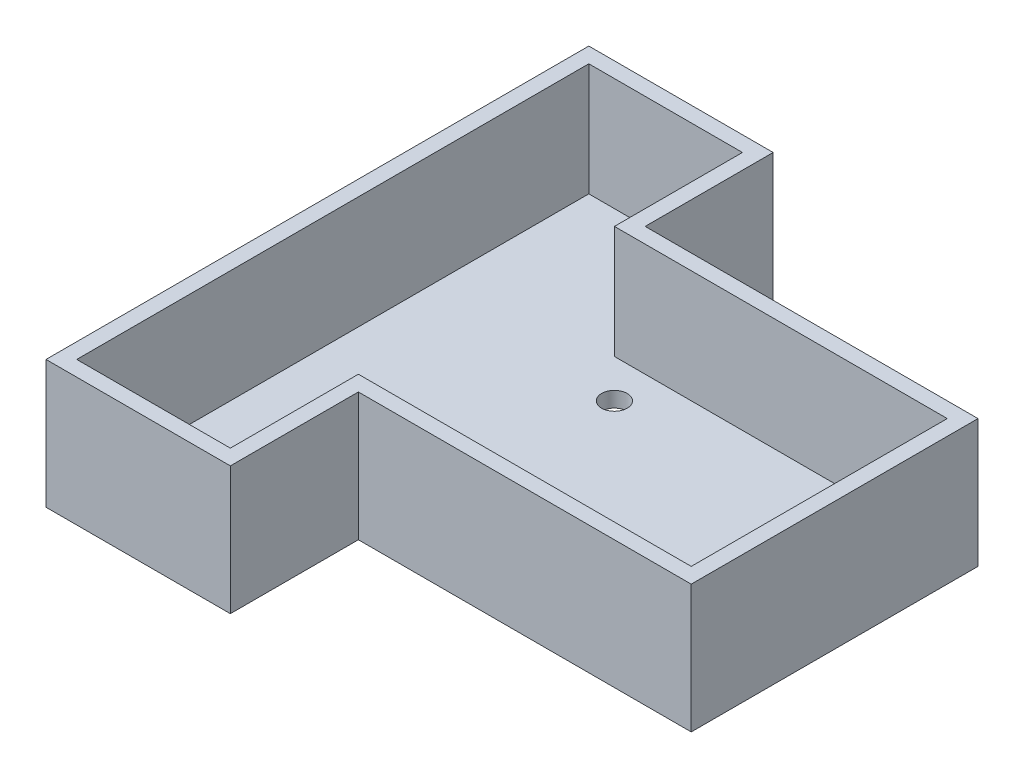
SolidWorks part; units mm, degrees
ref_plane "Front Plane" through (0, 0, 0) normal (0, 0, 1) x (1, 0, 0)
ref_plane "Top Plane" through (0, 0, 0) normal (0, 1, 0) x (1, 0, 0)
ref_plane "Right Plane" through (0, 0, 0) normal (1, 0, 0) x (0, 0, -1)
sketch "Sketch1" plane through (0, 0, 0) normal (0, 1, 0) x (1, 0, 0)
  line L12 (-32.5, 50) -> (-62.5, 50)
  line L13 (-62.5, 50) -> (-62.5, -50)
  line L14 (-62.5, -50) -> (-32.5, -50)
  line L25 (-32.5, -25) -> (-32.5, -50)
  line L32 (-32.5, 25) -> (32.5, 25)
  line L33 (32.5, 25) -> (32.5, -25)
  line L34 (32.5, -25) -> (-32.5, -25)
  line L36 (-32.5, 50) -> (-32.5, 25)
  line L37 (-29.5, 28) -> (35.5, 28)
  line L38 (35.5, 28) -> (35.5, -28)
  line L39 (35.5, -28) -> (-29.5, -28)
  line L40 (-29.5, -28) -> (-29.5, -53)
  line L41 (-65.5, -53) -> (-29.5, -53)
  line L42 (-65.5, 53) -> (-65.5, -53)
  line L43 (-29.5, 53) -> (-65.5, 53)
  line L44 (-29.5, 53) -> (-29.5, 28)
  circle A12 centre (-25, 17.5) radius 2.5
  circle A13 centre (25, 17.5) radius 2.5
  circle A14 centre (25, -17.5) radius 2.5
  circle A15 centre (-25, -17.5) radius 2.5
  dimension "D1" = 3
extrude "Boss-Extrude1" add sketch "Sketch1" along normal blind 25
sketch "Sketch6" plane through (0, 25, 0) normal (0, 1, 0) x (1, 0, 0)
  line L16 (-32.5, 25) -> (-32.5, 50)
  line L17 (-32.5, 50) -> (-62.5, 50)
  line L18 (-62.5, 50) -> (-62.5, -50)
  line L19 (-62.5, -50) -> (-32.5, -50)
  line L20 (-32.5, -50) -> (-32.5, -25)
  line L21 (-32.5, -25) -> (32.5, -25)
  line L22 (32.5, -25) -> (32.5, 25)
  line L23 (32.5, 25) -> (-32.5, 25)
  line L24 (-32.5, 25) -> (-32.5, 50)
  line L25 (-32.5, 50) -> (-62.5, 50)
  line L26 (-62.5, 50) -> (-62.5, -50)
  line L27 (-62.5, -50) -> (-32.5, -50)
  line L28 (-32.5, -50) -> (-32.5, -25)
  line L29 (-32.5, -25) -> (32.5, -25)
  line L30 (32.5, -25) -> (32.5, 25)
  line L31 (32.5, 25) -> (-32.5, 25)
  dimension "D1" = 3
extrude "Cut-Extrude2" cut sketch "Sketch6" against normal blind 22
